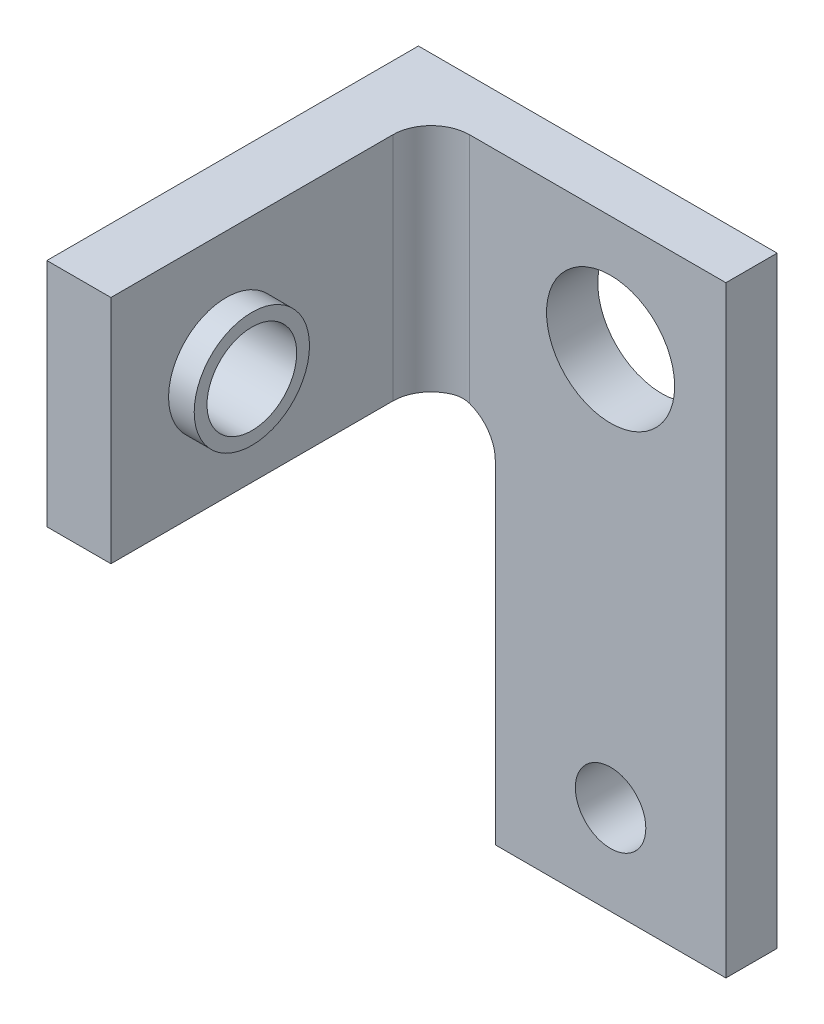
SolidWorks part; units mm, degrees
ref_plane "Front Plane" through (0, 0, 0) normal (0, 0, 1) x (1, 0, 0)
ref_plane "Top Plane" through (0, 0, 0) normal (0, 1, 0) x (1, 0, 0)
ref_plane "Right Plane" through (0, 0, 0) normal (1, 0, 0) x (0, 0, -1)
sketch "Sketch1" plane through (0, 0, 0) normal (0, 0, 1) x (1, 0, 0)
  line L1 (-4.5, -11) -> (4.5, -11)
  line L2 (-4.5, -11) -> (-4.5, 11)
  line L3 (-4.5, 11) -> (4.5, 11)
  line L4 (4.5, -11) -> (4.5, 11)
  point P0 (0, 0)
  dimension "D1" = 22
  dimension "D2" = 9
extrude "Boss-Extrude1" add sketch "Sketch1" along normal blind 2
sketch "Sketch2" plane through (0, 0, 2) normal (0, 0, 1) x (1, 0, 0)
  line L0 (4.5, -11) -> (4.5, 11) construction
  line L1 (4.5, 11) -> (-4.5, 11) construction
  line L2 (-4.5, -11) -> (4.5, -11) construction
  circle A0 centre (0, 6.5) radius 2.5
  circle A1 centre (0, -9) radius 1.375
  dimension "D1" = 5
  dimension "D4" = 2.75
  dimension "D2" = 4.5
  dimension "D3" = 4.5
  dimension "D5" = 4.5
  dimension "D6" = 2
extrude "Cut-Extrude1" cut sketch "Sketch2" against normal blind 2
sketch "Sketch3" plane through (-4.5, 0, 0) normal (-1, 0, 0) x (0, 0, 1)
  line L0 (0, 11) -> (0, -11) construction
  line L1 (2, 11) -> (0, 11)
  line L2 (2, 11) -> (2, 2)
  line L3 (2, 2) -> (0, 2)
  line L4 (0, 11) -> (0, 2)
  dimension "D1" = 9
extrude "Boss-Extrude2" add sketch "Sketch3" along normal blind 5
sketch "Sketch5" plane through (0, 0, 2) normal (0, 0, 1) x (1, 0, 0)
  line L0 (-9.5, 2) -> (-4.5, 2) construction
  line L1 (-9.5, 11) -> (-7, 11)
  line L2 (-9.5, 11) -> (-9.5, 2)
  line L3 (-9.5, 2) -> (-7, 2)
  line L4 (-7, 11) -> (-7, 2)
  dimension "D1" = 2.5
extrude "Boss-Extrude4" add sketch "Sketch5" along normal blind 12.5
sketch "Sketch6" plane through (-7, 0, 0) normal (1, 0, 0) x (0, 0, -1)
  line L0 (-14.5, 2) -> (-14.5, 11) construction
  line L1 (-14.5, 11) -> (-2, 11) construction
  circle A0 centre (-10, 6.5) radius 1.75
  dimension "D1" = 3.5
  dimension "D2" = 4.5
  dimension "D3" = 4.5
extrude "Cut-Extrude2" cut sketch "Sketch6" against normal blind 2.5
sketch "Sketch7" plane through (-7, 0, 0) normal (1, 0, 0) x (0, 0, -1)
  circle A0 centre (-10, 6.5) radius 2.25
  dimension "D1" = 4.5
extrude "Boss-Extrude5" add sketch "Sketch7" along normal blind 1
sketch "Sketch8" plane through (-6, 0, 0) normal (1, 0, 0) x (0, 0, -1)
  line L0 (-14.5, 11) -> (-2, 11) construction
  line L1 (-14.5, 2) -> (-14.5, 11) construction
  circle A0 centre (-10, 6.5) radius 1.75
  dimension "D1" = 3.5
  dimension "D2" = 4.5
  dimension "D3" = 4.5
extrude "Cut-Extrude3" cut sketch "Sketch8" against normal blind 1
sketch "Sketch9" plane through (-9.5, 0, 0) normal (-1, 0, 0) x (0, 0, 1)
  circle A0 centre (10, 6.5) radius 2.25
  dimension "D1" = 4.5
extrude "Boss-Extrude6" add sketch "Sketch9" along normal blind 1
sketch "Sketch10" plane through (-10.5, 0, 0) normal (-1, 0, 0) x (0, 0, 1)
  line L0 (0, 2) -> (14.5, 2) construction
  line L1 (14.5, 11) -> (14.5, 2) construction
  circle A0 centre (10, 6.5) radius 1.75
  dimension "D1" = 3.5
  dimension "D2" = 4.5
  dimension "D3" = 4.5
extrude "Cut-Extrude4" cut sketch "Sketch10" against normal blind 1
fillet "Fillet1" radius 1.5 1 edges at (-7, 6.5, 2)
fillet "Fillet2" radius 1.5 1 edges at (-4.5, 2, 1)
sketch "Sketch11" plane through (0, -11, 0) normal (0, -1, 0) x (1, 0, 0)
  line L1 (-4.5, 2) -> (4.5, 2)
  line L2 (-4.5, 2) -> (-4.5, 0)
  line L3 (-4.5, 0) -> (4.5, 0)
  line L4 (4.5, 2) -> (4.5, 0)
extrude "Boss-Extrude7" add sketch "Sketch11" along normal blind 1.5
